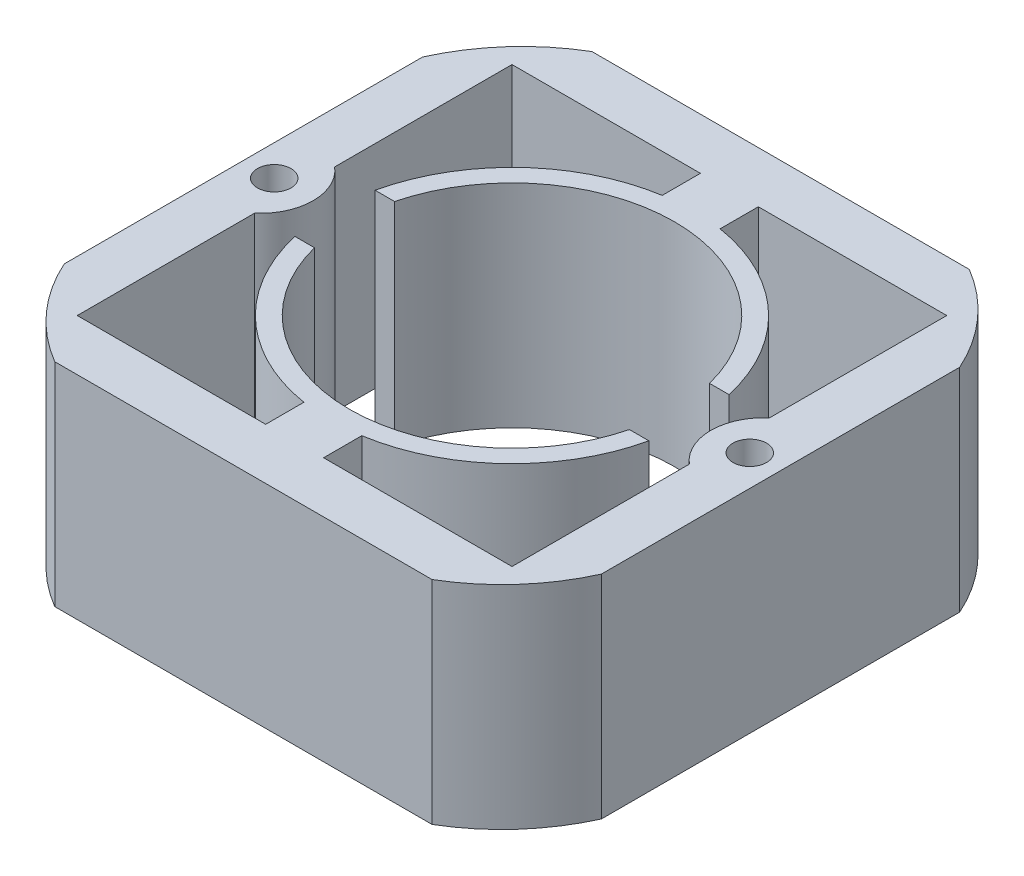
SolidWorks part; units mm, degrees
ref_plane "Front Plane" through (0, 0, 0) normal (0, 0, 1) x (1, 0, 0)
ref_plane "Top Plane" through (0, 0, 0) normal (0, 1, 0) x (1, 0, 0)
ref_plane "Right Plane" through (0, 0, 0) normal (1, 0, 0) x (0, 0, -1)
sketch "Sketch1" plane through (0, 0, 0) normal (0, 1, 0) x (1, 0, 0)
  line L0 (26.0287, 26.0286) -> (3.4666, 26.0286)
  line L1 (22.5891, -32.1627) -> (-22.5891, -32.1628)
  line L2 (32.1628, -21.4514) -> (32.1628, 21.4514)
  line L3 (22.5891, 32.1627) -> (-22.5891, 32.1627)
  line L4 (-32.1627, -21.4514) -> (-32.1628, 21.4514)
  line L5 (32.1628, -32.1628) -> (-32.1628, 32.1627) construction
  line L6 (32.1628, 32.1627) -> (-32.1628, -32.1628) construction
  line L7 (-26.0286, -26.0287) -> (-26.0287, -4.7948)
  line L8 (26.0287, -26.0287) -> (3.4666, -26.0287)
  line L9 (26.0287, -26.0287) -> (26.0287, -4.7948)
  line L10 (0, 0) -> (0, 16.3351) construction
  line L11 (26.0287, 4.7948) -> (26.0287, 26.0286)
  line L12 (-26.0287, 4.7948) -> (-26.0287, 26.0286)
  line L13 (26.0287, -26.0287) -> (26.0287, 26.0286) construction
  line L14 (26.0287, 4.7948) -> (-26.0287, 4.7948) construction
  line L15 (-26.0286, -26.0287) -> (-26.0287, 26.0286) construction
  line L16 (26.0287, -4.7948) -> (-26.0287, -4.7948) construction
  line L17 (21.1941, 4.7948) -> (18.8563, 4.7948)
  line L18 (21.1941, -4.7948) -> (18.8563, -4.7948)
  line L19 (3.4666, 16.3351) -> (-3.4666, 16.3351) construction
  line L20 (-21.1941, -4.7948) -> (-18.8563, -4.7948)
  line L21 (-18.8563, 4.7948) -> (-21.1941, 4.7948)
  line L22 (3.4666, 21.4514) -> (3.4666, 26.0286)
  line L23 (-3.4666, 21.4514) -> (-3.4666, 26.0286)
  line L24 (-3.4666, 26.0286) -> (-26.0287, 26.0286)
  line L25 (-3.4666, -26.0287) -> (-26.0286, -26.0287)
  line L26 (26.0287, 26.0286) -> (-26.0287, 26.0286) construction
  line L27 (0, 0) -> (16.4161, 0) construction
  line L28 (3.4666, -21.4514) -> (3.4666, -26.0287)
  line L29 (-3.4666, -21.4514) -> (-3.4666, -26.0287)
  line L30 (26.0287, -26.0287) -> (-26.0286, -26.0287) construction
  line L31 (32.1628, -32.1628) -> (32.1628, 32.1627) construction
  line L32 (32.1628, 32.1627) -> (-32.1628, 32.1627) construction
  line L33 (-32.1628, -32.1628) -> (-32.1628, 32.1627) construction
  line L35 (32.1628, -32.1628) -> (-32.1628, -32.1628) construction
  circle A0 centre (28.4734, 0) radius 2.0129
  circle A1 centre (-28.4734, 0) radius 2.0129
  arc A2 (26.0287, 4.7948) -> (26.0287, -4.7948) centre (30.1063, 0) ccw
  arc A3 (-26.0287, 4.7948) -> (-26.0287, -4.7948) centre (-30.1063, 0) cw
  arc A4 (18.8563, 4.7948) -> (-18.8563, 4.7948) centre (0, 0) ccw
  arc A5 (21.1941, 4.7948) -> (3.4666, 21.4514) centre (0, 0) ccw
  arc A6 (-18.8563, -4.7948) -> (18.8563, -4.7948) centre (0, 0) ccw
  circle A7 centre (0, 0) radius 21.7297 construction
  circle A8 centre (0, 0) radius 19.4564 construction
  arc A9 (-21.1941, -4.7948) -> (-3.4666, -21.4514) centre (0, 0) ccw
  arc A10 (-3.4666, 21.4514) -> (-21.1941, 4.7948) centre (0, 0) ccw
  arc A11 (3.4666, -21.4514) -> (21.1941, -4.7948) centre (0, 0) ccw
  arc A12 (32.1628, 21.4514) -> (22.5891, 32.1627) centre (10.5098, 11.7323) ccw
  arc A13 (-32.1628, 21.4514) -> (-22.5891, 32.1627) centre (-10.5098, 11.7323) cw
  arc A14 (-32.1627, -21.4514) -> (-22.5891, -32.1628) centre (-10.5098, -11.7323) ccw
  arc A15 (32.1628, -21.4514) -> (22.5891, -32.1627) centre (10.5098, -11.7323) cw
  point P7 (0, 0)
  point P16 (23.8121, 0)
  point P24 (18.6062, 5.6885)
  point P25 (21.7297, 0)
  point P38 (0, 16.3351)
  point P47 (3.4666, -23.74)
  point P50 (28.2058, 27.5488)
  dimension "D18" = 14.3662
  dimension "D21" = 53.6142
  dimension "D20" = 23.7342
  dimension "D2" = 4.0259
  dimension "D3" = 56.9468
  dimension "D1" = 4.0259
  dimension "D7" = 6.2942
  dimension "D9" = 38.9128
  dimension "D4" = 28.4734
  dimension "D10" = 2.2733
  dimension "D11" = 6.9331
  dimension "D12" = 16.3351
  dimension "D13" = 4.5772
  dimension "D14" = 6.9331
  dimension "D15" = 21.4514
  dimension "D16" = 21.4514
  dimension "D17" = 6.9331
  dimension "D19" = 39.4272
  dimension "D5" = 64.3255
  dimension "D6" = 6.1341
  dimension "D8" = 4.7948
extrude "Boss-Extrude1" add sketch "Sketch1" along normal blind 25.4 contours A15 L2 A12 L3 A13 L4 A14 L1 A1 A0 L28 A11 L18 A6 L20 A9 L29 L25 L7 A3 L12 L24 L23 A10 L21 A4 L17 A5 L22 L0 L11 A2 L9 L8
